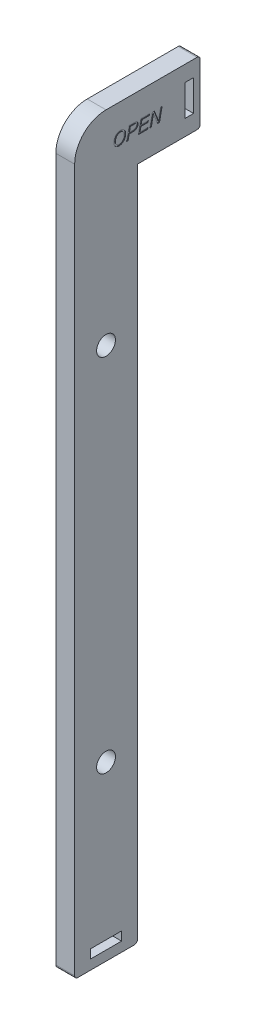
SolidWorks part; units mm, degrees
ref_plane "Спереди" through (0, 0, 0) normal (0, 0, 1) x (1, 0, 0)
ref_plane "Сверху" through (0, 0, 0) normal (0, 1, 0) x (1, 0, 0)
ref_plane "Справа" through (0, 0, 0) normal (1, 0, 0) x (0, 0, -1)
sketch "Эскиз1" plane through (0, 0, 0) normal (1, 0, 0) x (0, 0, -1)
  line L0 (0, 0) -> (0, 215)
  line L1 (0, 215) -> (20, 215)
  line L2 (20, 215) -> (20, 235)
  line L3 (20, 235) -> (-20, 235)
  line L4 (-20, 235) -> (-20, 0)
  line L5 (-20, 0) -> (0, 0)
  line L7 (15.095, 229.95) -> (17.905, 229.95)
  line L8 (15.095, 229.95) -> (15.095, 220.05)
  line L9 (15.095, 220.05) -> (17.905, 220.05)
  line L10 (17.905, 229.95) -> (17.905, 220.05)
  line L11 (15.095, 229.95) -> (17.905, 220.05) construction
  line L12 (15.095, 220.05) -> (17.905, 229.95) construction
  line L13 (-14.95, 5.905) -> (-5.05, 5.905)
  line L14 (-14.95, 5.905) -> (-14.95, 3.095)
  line L15 (-14.95, 3.095) -> (-5.05, 3.095)
  line L16 (-5.05, 5.905) -> (-5.05, 3.095)
  line L17 (-14.95, 5.905) -> (-5.05, 3.095) construction
  line L18 (-14.95, 3.095) -> (-5.05, 5.905) construction
  circle A0 centre (-10, 170) radius 3
  circle A1 centre (-10, 55) radius 3
  point P9 (16.5, 225)
  point P16 (-10, 4.5)
  point P21 (0, 0)
  point P22 (-10, 0)
  dimension "D6" = 6
  dimension "D1" = 20
  dimension "D2" = 55
  dimension "D3" = 40
  dimension "D4" = 20
  dimension "D5" = 45
  dimension "D7" = 10
  dimension "D9" = 115
  dimension "D10" = 2.81
  dimension "D11" = 9.9
  dimension "D12" = 3.5
  dimension "D13" = 10
  dimension "D14" = 2.81
  dimension "D15" = 9.9
  dimension "D16" = 4.5
  dimension "D8" = 2
extrude "Бобышка-Вытянуть1" add sketch "Эскиз1" along normal blind 6 contours L4 L5 L0 L1 L2 L3 A0
fillet "Скругление1" radius 1 4 edges at (3, 235, -20) (3, 215, -20) (3, 0, 0) (3, 0, 20)
fillet "Скругление2" radius 10 1 edges at (3, 235, 20)
sketch "Эскиз2" plane through (6, 0, 0) normal (1, 0, 0) x (0, 0, -1)
  line L0 (19, 235) -> (-10, 235) construction
  line L1 (20, 216) -> (20, 234) construction
  text T0 "OPEN"
  dimension "D1" = 12
  dimension "D2" = 28
extrude "Вырез-Вытянуть1" cut sketch "Эскиз2" against normal blind 0.2
